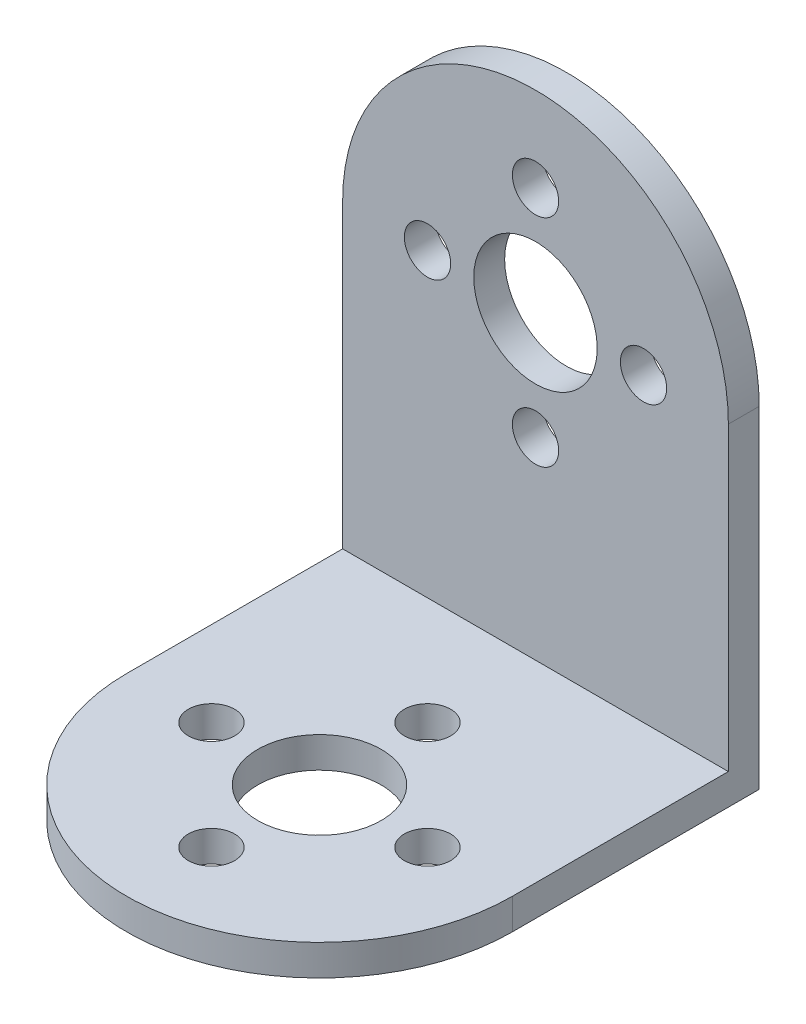
SolidWorks part; units mm, degrees
material "5052-H32"
ref_plane "Front Plane" through (0, 0, 0) normal (0, 0, 1) x (1, 0, 0)
ref_plane "Top Plane" through (0, 0, 0) normal (0, 1, 0) x (1, 0, 0)
ref_plane "Right Plane" through (0, 0, 0) normal (1, 0, 0) x (0, 0, -1)
sketch "Sketch1" plane through (0, 0, 0) normal (0, 1, 0) x (1, 0, 0)
  line L2 (12.5, -7) -> (12.5, 7)
  line L3 (12.5, 7) -> (-12.5, 7)
  line L4 (-12.5, -7) -> (-12.5, 7)
  line L5 (12.5, -7) -> (-12.5, 7) construction
  line L6 (12.5, 7) -> (-12.5, -7) construction
  arc A0 (-12.5, -7) -> (12.5, -7) centre (0, -7) ccw
  circle A1 centre (0, -7) radius 4
  circle A3 centre (0, 0) radius 1.5
  circle A4 centre (7, -7) radius 1.5
  circle A5 centre (-7, -7) radius 1.5
  circle A6 centre (0, -14) radius 1.5
  point P0 (0, 0)
  dimension "D3" = 3
  dimension "D4" = 3
  dimension "D5" = 3
  dimension "D6" = 3
  dimension "D7" = 7
  dimension "D8" = 8
  dimension "D1" = 14
  dimension "D2" = 25
  dimension "D9" = 14
  dimension "D10" = 7
  dimension "D11" = 7
extrude "Boss-Extrude1" add sketch "Sketch1" along normal blind 2
sketch "Sketch2" plane through (0, 0, -7) normal (0, 0, -1) x (-1, 0, 0)
  line L1 (-12.5, 0) -> (12.5, 0)
  line L2 (-12.5, 0) -> (-12.5, 21.5)
  line L4 (12.5, 0) -> (12.5, 21.5)
  arc A0 (-12.5, 21.5) -> (12.5, 21.5) centre (0, 21.5) cw
  circle A2 centre (0, 21.5) radius 4
  circle A3 centre (0, 28.5) radius 1.5
  circle A4 centre (7, 21.5) radius 1.5
  circle A5 centre (0, 14.5) radius 1.5
  circle A6 centre (-7, 21.5) radius 1.5
  dimension "D3" = 3
  dimension "D4" = 3
  dimension "D5" = 3
  dimension "D6" = 3
  dimension "D8" = 8
  dimension "D1" = 21.5
  dimension "D2" = 25
extrude "Boss-Extrude2" add sketch "Sketch2" along normal blind 2
